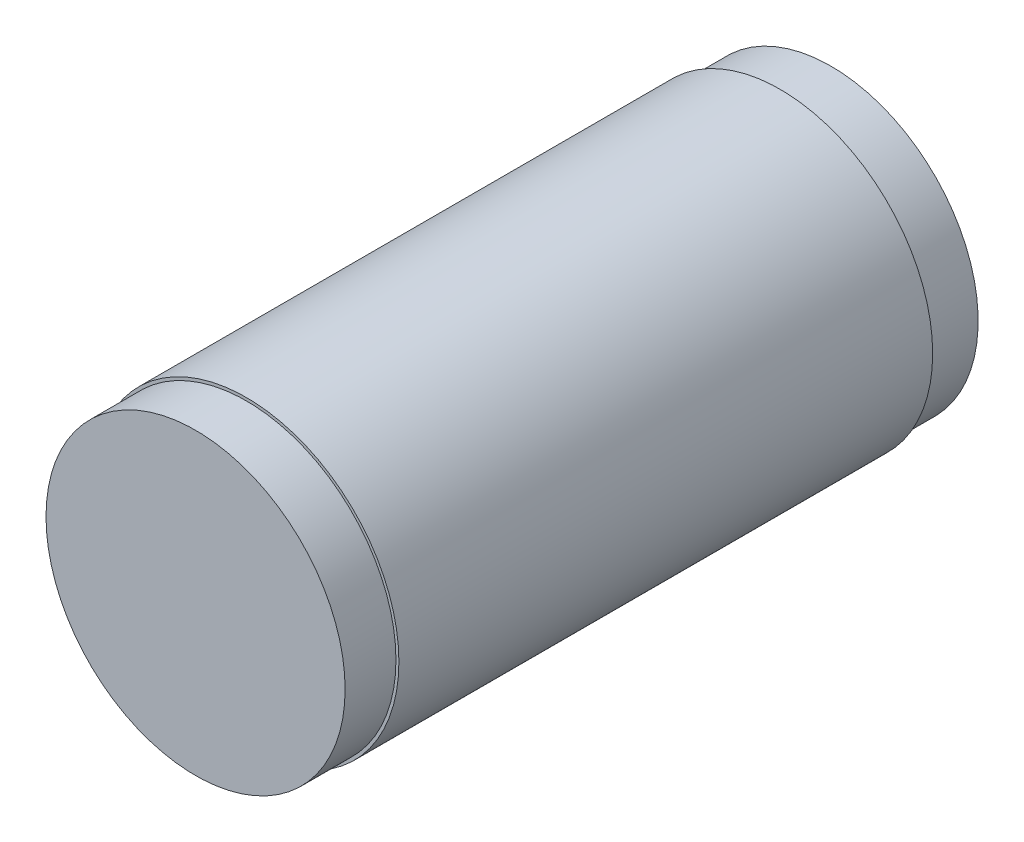
SolidWorks part; units mm, degrees
material "Ti-6Al-2Sn-2Zr-2Mo-2Cr-0.25Si (SS)"
ref_plane "Front Plane" through (0, 0, 0) normal (0, 0, 1) x (1, 0, 0)
ref_plane "Top Plane" through (0, 0, 0) normal (0, 1, 0) x (1, 0, 0)
ref_plane "Right Plane" through (0, 0, 0) normal (1, 0, 0) x (0, 0, -1)
sketch "Sketch1" plane through (0, 0, 0) normal (0, 0, 1) x (1, 0, 0)
  circle A0 centre (0, 0) radius 25
  circle A1 centre (0, 0) radius 30
  dimension "D1" = 50
  dimension "D2" = 60
extrude "Boss-Extrude1" add sketch "Sketch1" along normal blind 125
sketch "Sketch2" plane through (0, 0, 0) normal (0, 0, 1) x (1, 0, 0)
  circle A0 centre (0, 0) radius 21.1
  circle A1 centre (0, 0) radius 25
  dimension "D1" = 42.2
  dimension "D2" = 50
extrude "Boss-Extrude2" add sketch "Sketch2" along normal blind 10
ref_plane "Plane1" through (0, 0, 115) normal (0, 0, 1) x (1, 0, 0)
sketch "Sketch3" plane through (0, 0, 115) normal (0, 0, 1) x (1, 0, 0)
  circle A0 centre (0, 0) radius 25
  dimension "D1" = 50
extrude "Boss-Extrude3" add sketch "Sketch3" along normal blind 10
sketch "Sketch11" plane through (0, 0, 0) normal (0, 0, -1) x (-1, 0, 0)
  circle A0 centre (0, 0) radius 28.946
  circle A1 centre (0, 0) radius 30
extrude "Cut-Extrude2" cut sketch "Sketch11" against normal blind 10
sketch "Sketch12" plane through (0, 0, 125) normal (0, 0, 1) x (1, 0, 0)
  circle A0 centre (0, 0) radius 30
  circle A1 centre (0, 0) radius 29.421
extrude "Cut-Extrude3" cut sketch "Sketch12" against normal blind 10
ref_plane "Plane4" through (0, 0, 125) normal (0, 0, 1) x (1, 0, 0)
